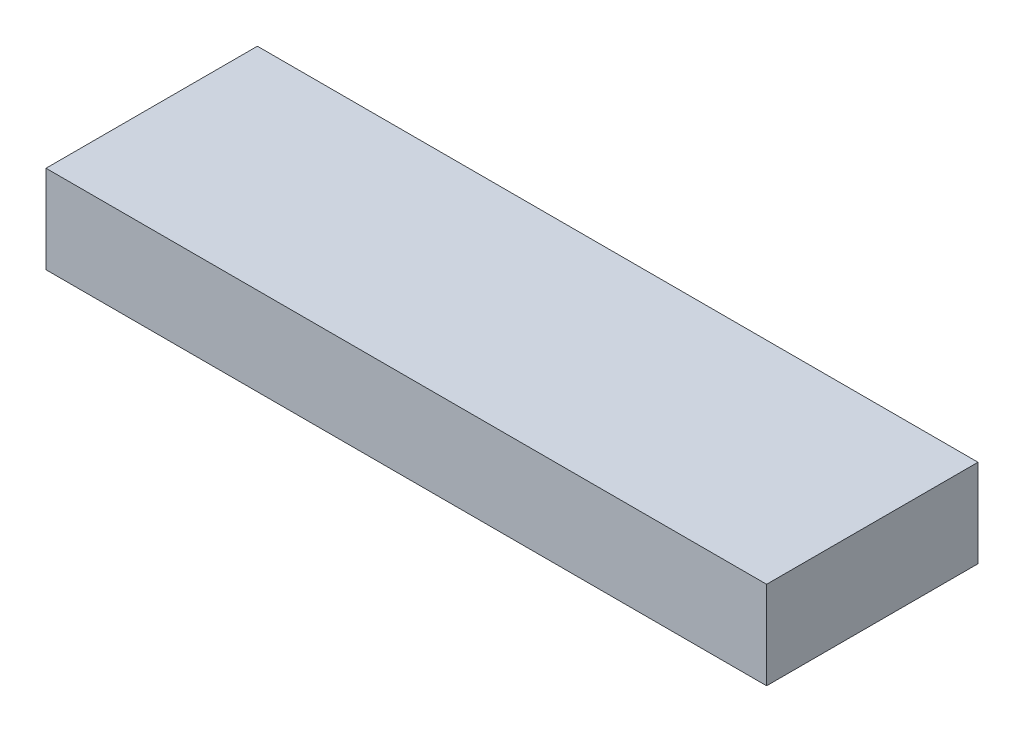
SolidWorks part; units mm, degrees
material "ABS"
ref_plane "Front Plane" through (0, 0, 0) normal (0, 0, 1) x (1, 0, 0)
ref_plane "Top Plane" through (0, 0, 0) normal (0, 1, 0) x (1, 0, 0)
ref_plane "Right Plane" through (0, 0, 0) normal (1, 0, 0) x (0, 0, -1)
sketch "Sketch1" plane through (0, 0, 0) normal (0, 0, 1) x (1, 0, 0)
  line L1 (9971.7909, 3457.4921) -> (7926.4917, 3457.4921)
  line L2 (9971.7909, 3457.4921) -> (9971.7909, 3207.9331)
  line L3 (9971.7909, 3207.9331) -> (7926.4917, 3207.9331)
  line L4 (7926.4917, 3457.4921) -> (7926.4917, 3207.9331)
extrude "Boss-Extrude1" add sketch "Sketch1" along normal blind 600
